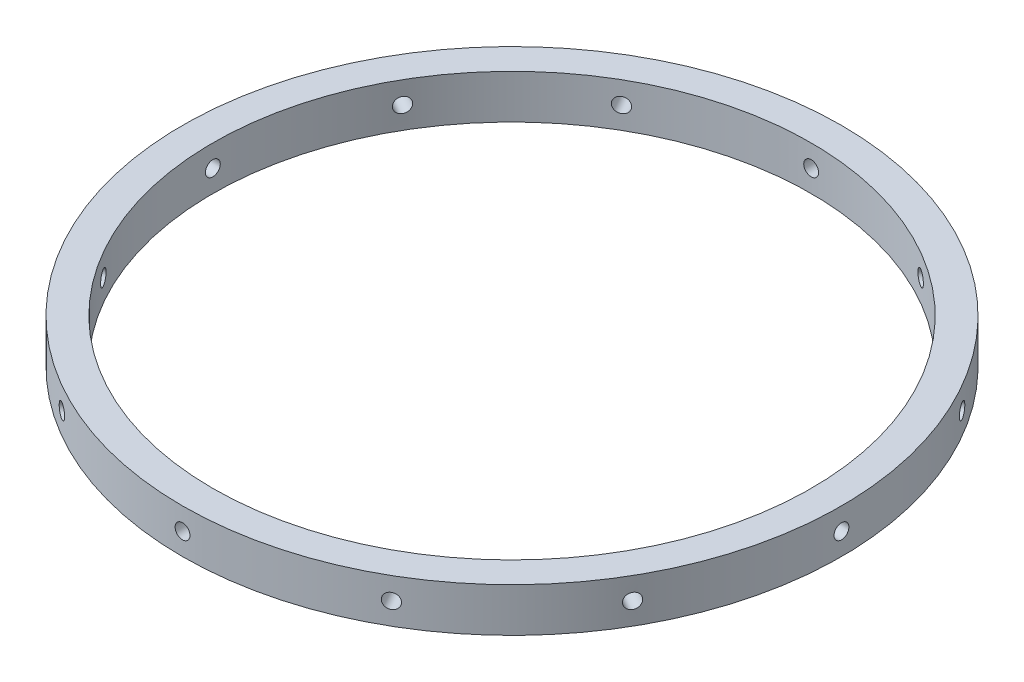
SolidWorks part; units mm, degrees
ref_plane "Front Plane" through (0, 0, 0) normal (0, 0, 1) x (1, 0, 0)
ref_plane "Top Plane" through (0, 0, 0) normal (0, 1, 0) x (1, 0, 0)
ref_plane "Right Plane" through (0, 0, 0) normal (1, 0, 0) x (0, 0, -1)
sketch "Sketch1" plane through (0, 0, 0) normal (0, 1, 0) x (1, 0, 0)
  circle A0 centre (0, 0) radius 95.25
  circle A1 centre (0, 0) radius 86.487
  dimension "D1" = 190.5
  dimension "D2" = 172.974
extrude "Boss-Extrude1" add sketch "Sketch1" along normal blind 12.7
sketch "Sketch3" plane through (0, 0, 0) normal (0, 0, 1) x (1, 0, 0)
  circle A0 centre (0, 6.35) radius 2.1463
  dimension "D1" = 4.2926
  dimension "D2" = 6.35
extrude "Cut-Extrude2" cut sketch "Sketch3" against normal blind 254
pattern_circular "CirPattern1" count 12 over 360 about axis through (0, 12.7, 0) along (0, 1, 0) of "Cut-Extrude2"
